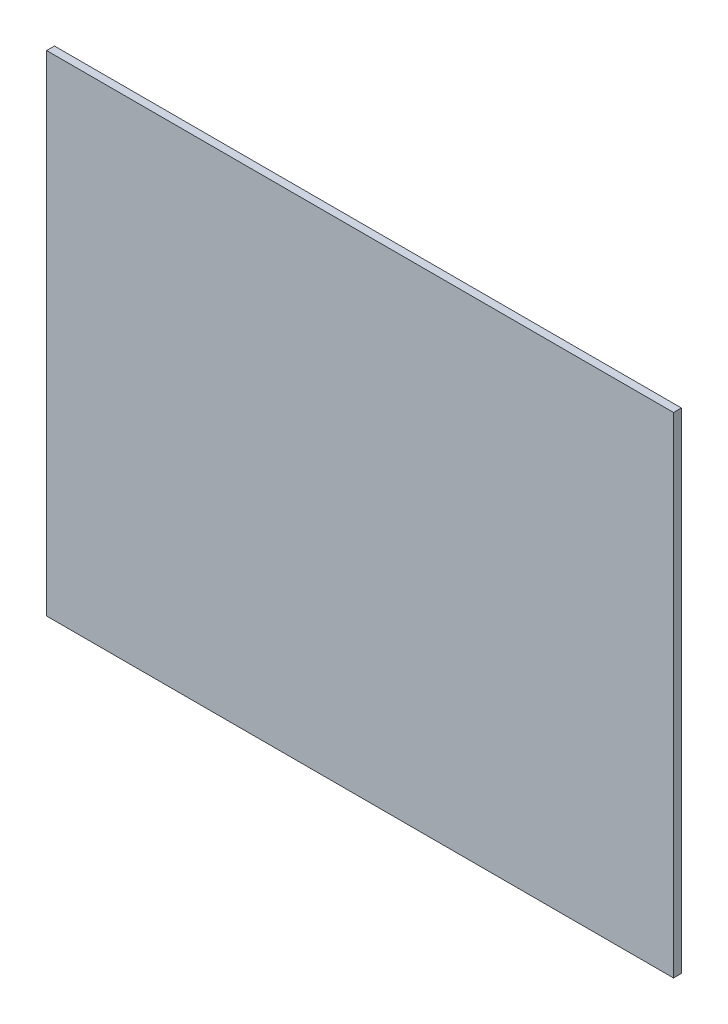
SolidWorks part; units mm, degrees
material "Cobre"
ref_plane "Plano frontal" through (0, 0, 0) normal (0, 0, 1) x (1, 0, 0)
ref_plane "Plano superior" through (0, 0, 0) normal (0, 1, 0) x (1, 0, 0)
ref_plane "Plano direito" through (0, 0, 0) normal (1, 0, 0) x (0, 0, -1)
sketch "Esboço1" plane through (0, 0, 0) normal (0, 0, 1) x (1, 0, 0)
  line L1 (52.3676, -148.0271) -> (-107.6324, -148.0271)
  line L2 (52.3676, -148.0271) -> (52.3676, -23.0271)
  line L3 (52.3676, -23.0271) -> (-107.6324, -23.0271)
  line L4 (-107.6324, -148.0271) -> (-107.6324, -23.0271)
  dimension "D1" = 160
  dimension "D2" = 125
extrude "Ressalto-extrusão1" add sketch "Esboço1" along normal blind 2
